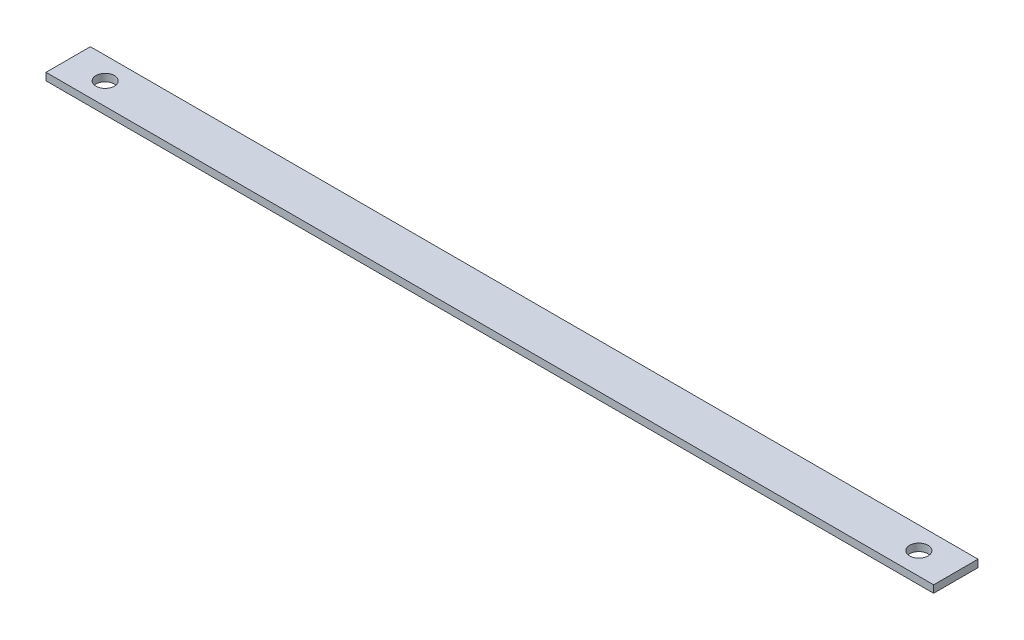
SolidWorks part; units mm, degrees
ref_plane "Front Plane" through (0, 0, 0) normal (0, 0, 1) x (1, 0, 0)
ref_plane "Top Plane" through (0, 0, 0) normal (0, 1, 0) x (1, 0, 0)
ref_plane "Right Plane" through (0, 0, 0) normal (1, 0, 0) x (0, 0, -1)
sketch "Sketch1" plane through (0, 0, 0) normal (0, 1, 0) x (1, 0, 0)
  line L1 (-120, -6) -> (120, -6)
  line L2 (-120, -6) -> (-120, 6)
  line L3 (-120, 6) -> (120, 6)
  line L4 (120, -6) -> (120, 6)
  line L5 (-120, -6) -> (120, 6) construction
  line L6 (-120, 6) -> (120, -6) construction
  point P0 (0, 0)
  dimension "D1" = 12
  dimension "D2" = 240
extrude "Boss-Extrude1" add sketch "Sketch1" along normal blind 2
sketch "Sketch2" plane through (0, 2, 0) normal (0, 1, 0) x (1, 0, 0)
  line L0 (-93.3786, 0) -> (99.7379, 0) construction
  line L1 (0, 28.8342) -> (0, -18.9283) construction
  point P5 (110, 0)
  point P6 (-110, 0)
  dimension "D1" = 110
hole_wizard "Ø5.0mm Dowel Hole1" positions "Sketch3" profile "Sketch4" hole size "Ø5.0" standard "ANSI Metric" end condition up to next
sketch "Sketch3" plane through (0, 2, 0) normal (0, 1, 0) x (1, 0, 0)
  point P0 (-110, 0)
  point P3 (110, 0)
sketch "Sketch4" plane through (-110, 2, 0) normal (1, 0, 0) x (0, 0, 1)
  line L0 (0, 0) -> (0, 2)
  line L1 (0, 2) -> (2.5, 2)
  line L2 (2.5, 2) -> (2.5, 0)
  line L5 (2.5, 0) -> (0, 0)
  line L11 (0, -6.35) -> (0, 107.95) construction
  dimension "Thru Hole Dia." = 5
  dimension "Thru Hole Depth" = 2
equation "\"Width\"=12"
equation "\"Length\"= 220"
equation "\"D2@Sketch1\"=\"Length\"+20"
equation "\"thick\"= 2"
equation "\"D1@Boss-Extrude1\"=\"thick\""
equation "\"D1@Sketch2\"=\"Length\"/2"
equation "\"D1@Sketch1\"=\"Width\""
